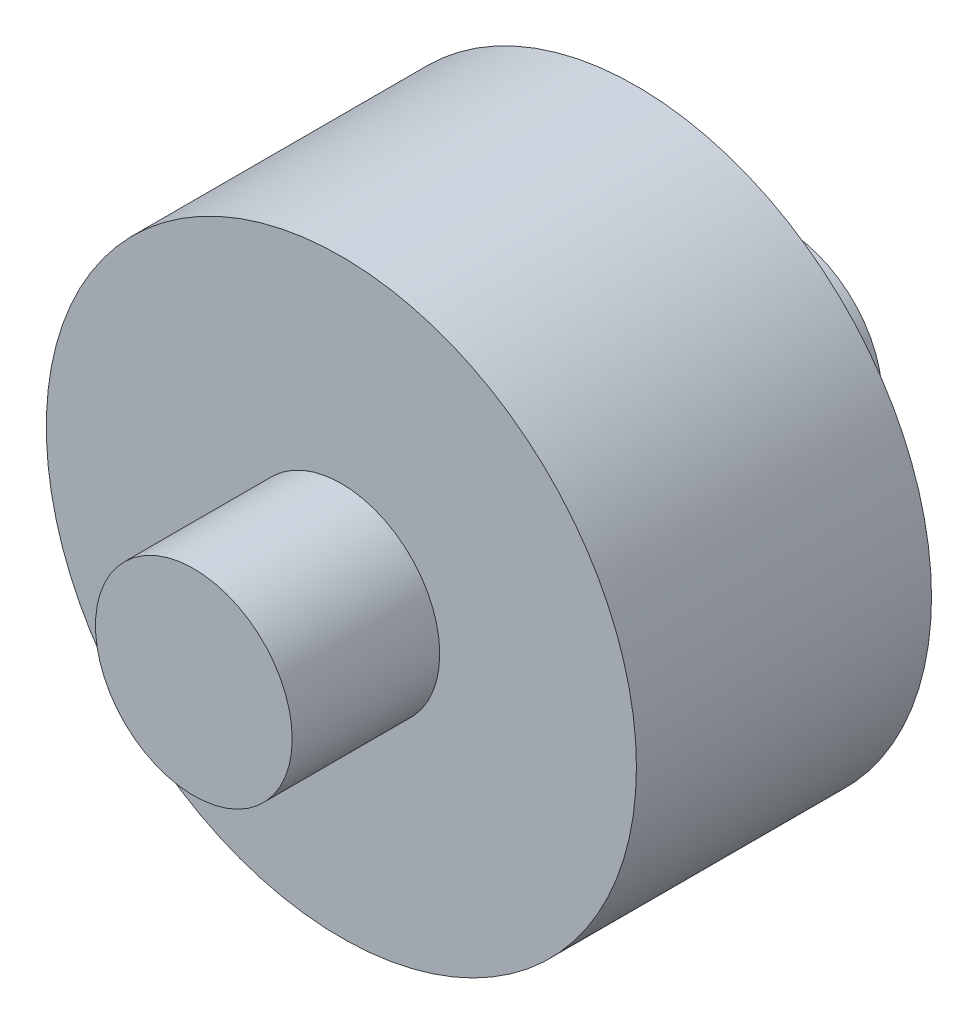
SolidWorks part; units mm, degrees
ref_plane "Front Plane" through (0, 0, 0) normal (0, 0, 1) x (1, 0, 0)
ref_plane "Top Plane" through (0, 0, 0) normal (0, 1, 0) x (1, 0, 0)
ref_plane "Right Plane" through (0, 0, 0) normal (1, 0, 0) x (0, 0, -1)
sketch "Sketch2" plane through (0, 0, 0) normal (0, 0, 1) x (1, 0, 0)
  circle A0 centre (0, 0) radius 9.525
  dimension "D1" = 19.05
extrude "Boss-Extrude2" add sketch "Sketch2" along normal mid plane 9.525
sketch "Sketch5" plane through (0, 0, 0) normal (0, 0, 1) x (1, 0, 0)
  circle A0 centre (0, 0) radius 3.175
  dimension "D1" = 6.35
extrude "Boss-Extrude3" add sketch "Sketch5" along normal mid plane 19.05 contours A0
sketch "Sketch6" plane through (0, 0, 0) normal (1, 0, 0) x (0, 0, -1)
  circle A0 centre (0, 0) radius 3.175
  dimension "D1" = 6.35
extrude "Cut-Extrude3" cut sketch "Sketch6" against normal through all contours A0
